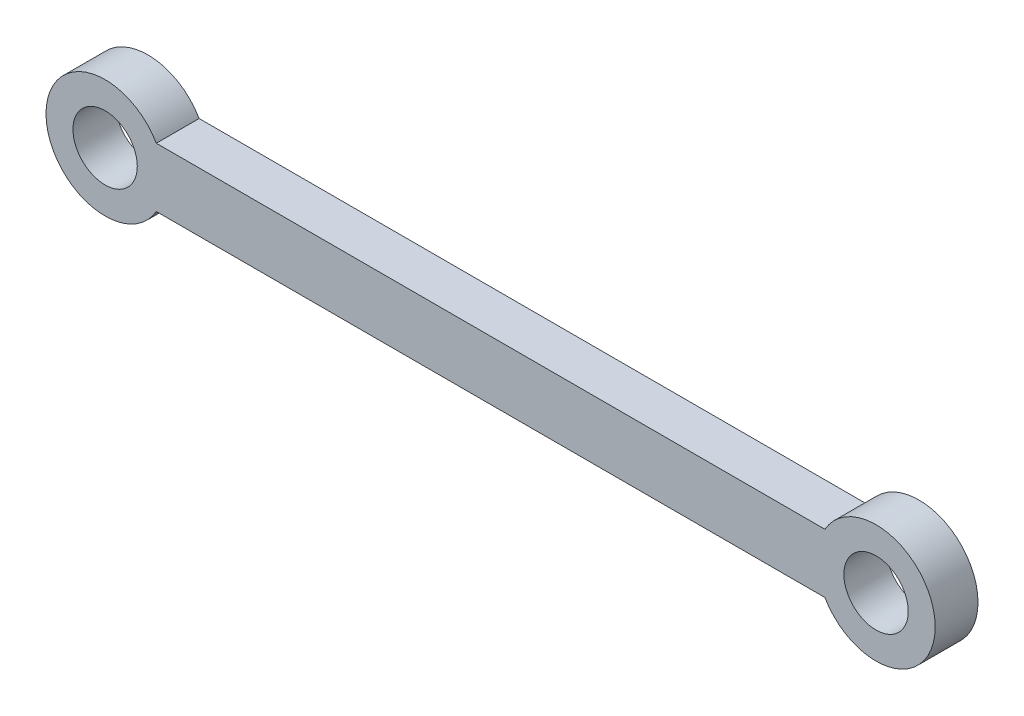
SolidWorks part; units mm, degrees
ref_plane "Front Plane" through (0, 0, 0) normal (0, 0, 1) x (1, 0, 0)
ref_plane "Top Plane" through (0, 0, 0) normal (0, 1, 0) x (1, 0, 0)
ref_plane "Right Plane" through (0, 0, 0) normal (1, 0, 0) x (0, 0, -1)
sketch "Sketch1" plane through (0, 0, 0) normal (0, 0, 1) x (1, 0, 0)
  line L0 (-45, 0) -> (45, 0) construction
  line L1 (0, 9.3204) -> (0, -7.6825) construction
  line L2 (-45, 0) -> (-39.0235, 3.4505) construction
  line L3 (-39.0235, 3.4505) -> (39.0235, 3.4505)
  line L4 (-39.0235, -3.4505) -> (39.0235, -3.4505)
  arc A0 (-39.0235, 3.4505) -> (-39.0235, -3.4505) centre (-45, 0) ccw
  circle A1 centre (-45, 0) radius 3.7565
  arc A2 (39.0235, 3.4505) -> (39.0235, -3.4505) centre (45, 0) cw
  circle A3 centre (45, 0) radius 3.7565
  dimension "D1" = 30
  dimension "70" = 90
extrude "Boss-Extrude1" add sketch "Sketch1" along normal blind 5
